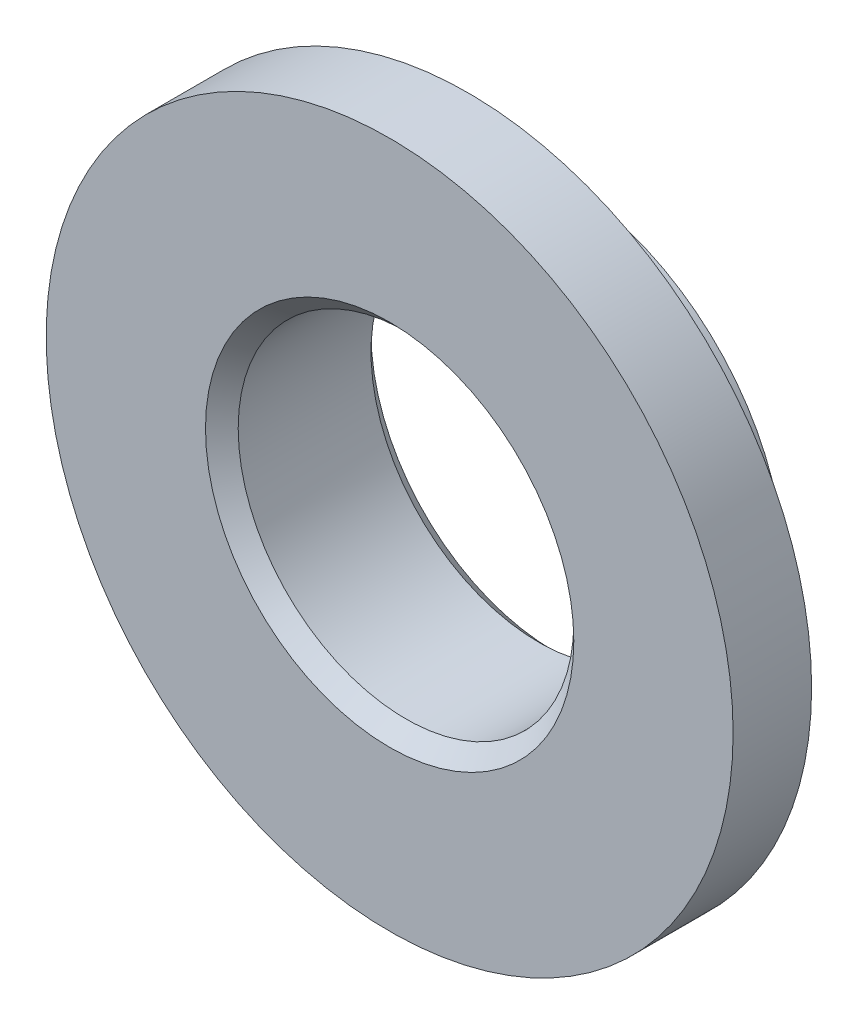
SolidWorks part; units mm, degrees
ref_plane "Plan de face" through (0, 0, 0) normal (0, 0, 1) x (1, 0, 0)
ref_plane "Plan de dessus" through (0, 0, 0) normal (0, 1, 0) x (1, 0, 0)
ref_plane "Plan de droite" through (0, 0, 0) normal (1, 0, 0) x (0, 0, -1)
sketch "Esquisse1" plane through (0, 0, 0) normal (1, 0, 0) x (0, 0, -1)
  line L0 (0, 0) -> (5.06, 0) construction
  line L1 (0, 10.5) -> (0, 5.13)
  line L2 (0, 5.13) -> (5.06, 5.13)
  line L3 (5.06, 7) -> (2.4, 7)
  line L4 (5.06, 5.13) -> (5.06, 7)
  line L5 (2.4, 7) -> (2.4, 10.5)
  line L6 (2.4, 10.5) -> (0, 10.5)
  dimension "D1" = 5.13
  dimension "D2" = 5.06
  dimension "D3" = 10.5
  dimension "D4" = 7
  dimension "D5" = 2.4
revolve "Révolution1" add sketch "Esquisse1" angle 360 about L0
chamfer "Chanfrein1" distance 0.5 angle 45 1 edges at (5.13, 0, 0)
chamfer "Chanfrein2" distance 0.5 angle 45 1 edges at (5.13, 0, -5.06)
equation "\"D1@Esquisse1\"=10.26/2"
equation "\"D2@Esquisse1\"=4.26+0.8"
equation "\"D3@Esquisse1\"=21/2"
equation "\"D4@Esquisse1\"=14/2"
equation "\"D5@Esquisse1\"=1.6+0.8"
